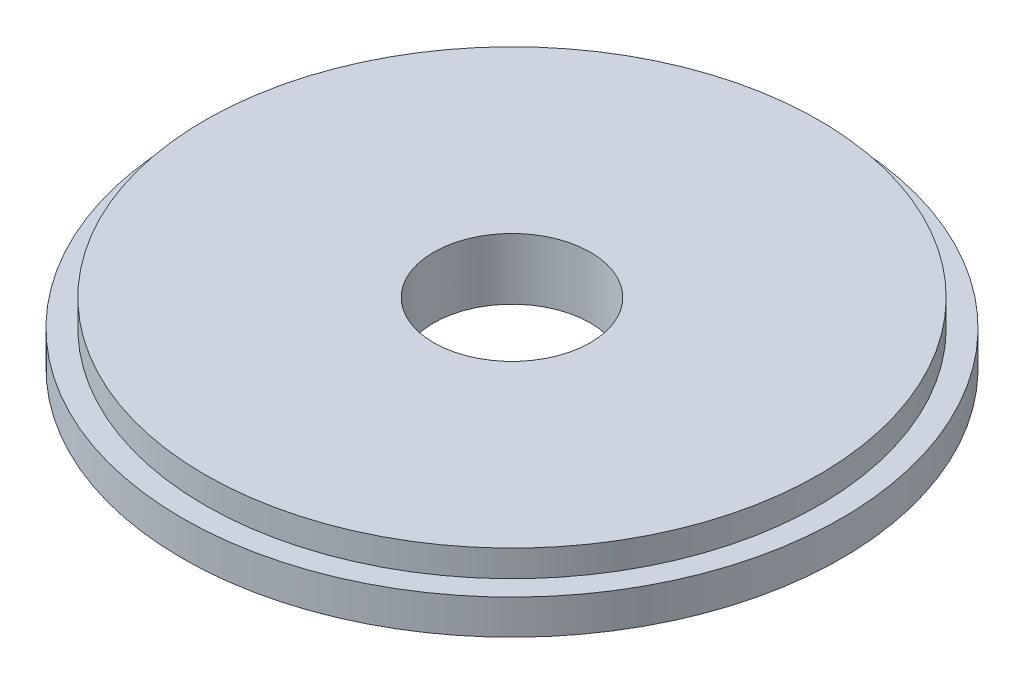
SolidWorks part; units mm, degrees
ref_plane "Front Plane" through (0, 0, 0) normal (0, 0, 1) x (1, 0, 0)
ref_plane "Top Plane" through (0, 0, 0) normal (0, 1, 0) x (1, 0, 0)
ref_plane "Right Plane" through (0, 0, 0) normal (1, 0, 0) x (0, 0, -1)
sketch "Sketch1" plane through (0, 0, 0) normal (0, 1, 0) x (1, 0, 0)
  circle A0 centre (0, 0) radius 27.325
  dimension "D1" = 54.65
extrude "Boss-Extrude1" add sketch "Sketch1" along normal blind 2.8829
sketch "Sketch2" plane through (0, 2.8829, 0) normal (0, 1, 0) x (1, 0, 0)
  circle A0 centre (0, 0) radius 25.4572
  dimension "D1" = 50.9143
extrude "Boss-Extrude2" add sketch "Sketch2" along normal blind 2.1971
sketch "Sketch6" plane through (0, 0, 0) normal (0, -1, 0) x (1, 0, 0)
  circle A0 centre (0, 0) radius 6.5006
extrude "Cut-Extrude1" cut sketch "Sketch6" against normal blind 25.4
